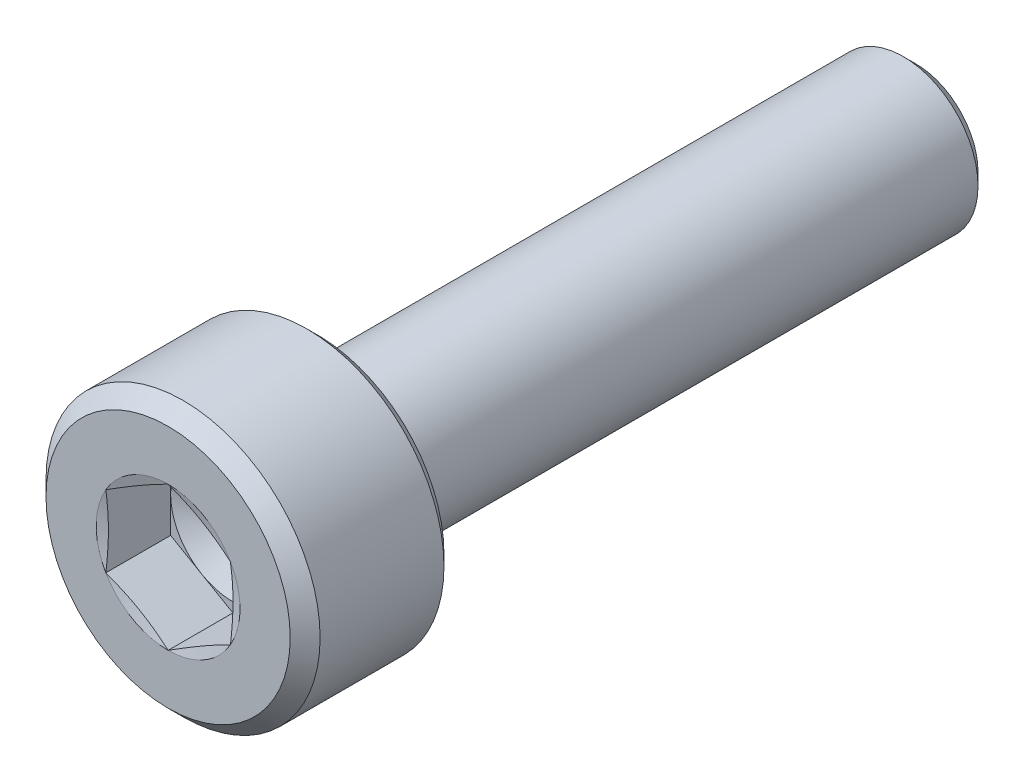
SolidWorks part; units mm, degrees
ref_plane "Front Plane" through (0, 0, 0) normal (0, 0, 1) x (1, 0, 0)
ref_plane "Top Plane" through (0, 0, 0) normal (0, 1, 0) x (1, 0, 0)
ref_plane "Right Plane" through (0, 0, 0) normal (1, 0, 0) x (0, 0, -1)
sketch "Sketch1" plane through (0, 0, 0) normal (1, 0, 0) x (0, 0, -1)
  line L0 (0, 0) -> (12.9407, 0) construction
  line L1 (0, 0) -> (0, 2.45)
  line L2 (0, 2.45) -> (0.3, 2.75)
  line L3 (0.3, 2.75) -> (2.785, 2.75)
  line L4 (3, 2.535) -> (3, 1.8)
  line L5 (3.51, 1.5) -> (14.75, 1.5)
  line L6 (14.75, 1.5) -> (15, 1.25)
  line L7 (15, 1.25) -> (15, 0)
  line L8 (15, 0) -> (0, 0)
  line L9 (2.785, 2.75) -> (3, 2.535)
  line L10 (3.4662, 1.5101) -> (3.0562, 1.7101)
  arc A2 (3.51, 1.5) -> (3.4662, 1.5101) centre (3.51, 1.6) cw
  arc A3 (3.0562, 1.7101) -> (3, 1.8) centre (3.1, 1.8) cw
  point P6 (3, 2.75)
  dimension "R2" = 0.1
  dimension "R1" = 0.1
  dimension "D1" = 45
  dimension "DK" = 5.5
  dimension "D3" = 45
  dimension "length" = 12
  dimension "K" = 3
  dimension "V" = 0.3
  dimension "HOLESIZE" = 3
  dimension "D4" = 2.5
  dimension "D5" = 45
  dimension "DW" = 5.07
  dimension "F" = 0.51
  dimension "DA" = 3.6
revolve "Revolve1" add sketch "Sketch1" angle 360 about L0
cosmetic thread "Cosmetic Thread1" parameters "D1"=10.5, "D2"=3
sketch "Sketch2" plane through (0, 0, 0) normal (0, 0, 1) x (1, 0, 0)
  line L0 (0, 0) -> (0, 1.4434) construction
  line L2 (0, 1.4434) -> (-1.25, 0.7217)
  line L3 (-1.25, 0.7217) -> (-1.25, -0.7217)
  line L4 (-1.25, -0.7217) -> (0, -1.4434)
  line L5 (0, -1.4434) -> (1.25, -0.7217)
  line L6 (1.25, -0.7217) -> (1.25, 0.7217)
  line L7 (1.25, 0.7217) -> (0, 1.4434)
  circle A0 centre (0, 0) radius 1.25 construction
  dimension "S" = 2.5
extrude "Cut-Extrude1" cut sketch "Sketch2" against normal blind 1.3
sketch "Sketch3" plane through (0, 0, 0) normal (1, 0, 0) x (0, 0, -1)
  line L0 (1.3, 0) -> (15, 0) construction
  line L1 (15, -1.25) -> (15, 1.25) construction
  line L2 (1.3, 0) -> (1.3, 1.25)
  line L4 (1.3, 1.25) -> (2.0217, 0)
  line L5 (2.0217, 0) -> (1.3, 0)
  line L6 (0, 2.45) -> (0, -2.45) construction
  dimension "DRILLANG" = 60
  dimension "DRILL DEPTH" = 1.3
  dimension "S2" = 2.5
revolve "Cut-Revolve2" cut sketch "Sketch3" angle 360 about L0
sketch "Sketch4" plane through (0, 0, 0) normal (1, 0, 0) x (0, 0, -1)
  line L0 (0, 0) -> (4.6121, 0) construction
  line L1 (0, 1.4434) -> (0, 1.25)
  line L2 (0, 2.45) -> (0, -2.45) construction
  line L3 (0, 1.25) -> (0.0518, 1.25)
  line L4 (0.0518, 1.25) -> (0, 1.4434)
  point P12 (0.0259, 1.25)
  dimension "D1" = 2.5
  dimension "D2" = 15
revolve "Cut-Revolve3" cut sketch "Sketch4" angle 360 about L0
